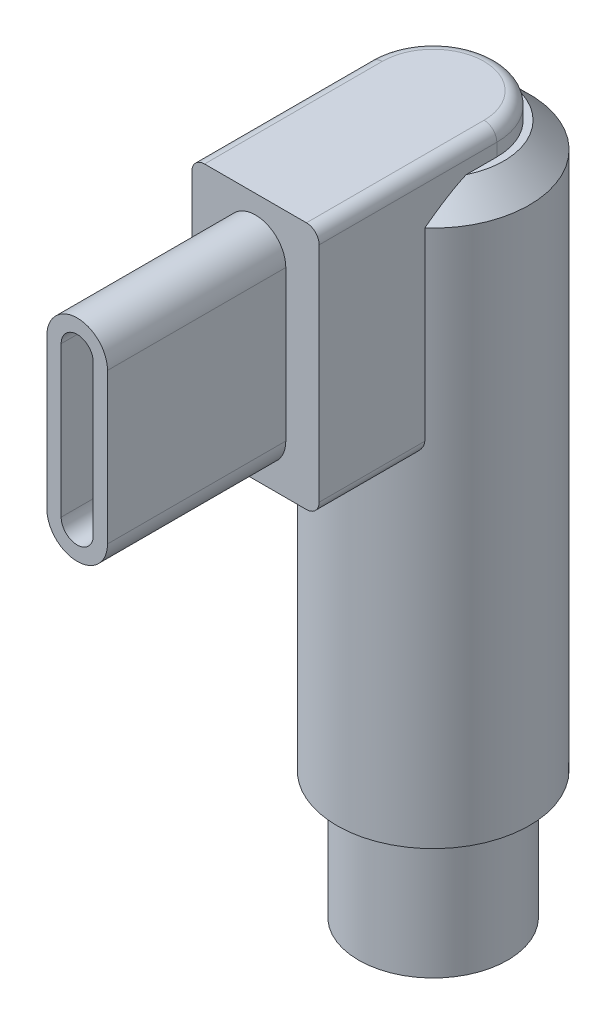
SolidWorks part; units mm, degrees
ref_plane "Front" through (0, 0, 0) normal (0, 0, 1) x (1, 0, 0)
ref_plane "Top" through (0, 0, 0) normal (0, 1, 0) x (1, 0, 0)
ref_plane "Right" through (0, 0, 0) normal (1, 0, 0) x (0, 0, -1)
sketch "Sketch1" plane through (0, 0, 0) normal (0, 1, 0) x (1, 0, 0)
  circle A0 centre (0, 0) radius 2.925
  dimension "D1" = 5.85
extrude "Boss-Extrude1" add sketch "Sketch1" along normal blind 5
sketch "Sketch2" plane through (0, 5, 0) normal (0, 1, 0) x (1, 0, 0)
  circle A0 centre (0, 0) radius 3.775
  dimension "D1" = 7.55
extrude "Boss-Extrude2" add sketch "Sketch2" along normal blind 23.1
ref_plane "Plane1" through (0, 0, 3.775) normal (0, 0, 1) x (1, 0, 0)
sketch "Sketch3" plane through (0, 0, 3.775) normal (0, 0, 1) x (1, 0, 0)
  line L0 (3.775, 28.1) -> (-3.775, 28.1) construction
  line L1 (-2.5, 28.1) -> (2.5, 28.1)
  line L2 (-2.5, 28.1) -> (-2.5, 18.35)
  line L3 (-2.5, 18.35) -> (2.5, 18.35)
  line L4 (2.5, 28.1) -> (2.5, 18.35)
  point P4 (0, 28.1)
  dimension "D1" = 5
  dimension "D2" = 9.75
extrude "Boss-Extrude3" add sketch "Sketch3" along normal blind 3.2 and the other way up to next
sketch "Sketch4" plane through (0, 0, 6.975) normal (0, 0, 1) x (1, 0, 0)
  line L0 (0, 26.175) -> (0, 20.275) construction
  line L1 (1.19, 26.175) -> (1.19, 20.275)
  line L2 (-1.19, 26.175) -> (-1.19, 20.275)
  line L3 (-2.5, 23.225) -> (0, 23.225) construction
  line L4 (-2.5, 28.1) -> (-2.5, 18.35) construction
  line L5 (0, 26.175) -> (0, 20.275) construction
  line L6 (0.63, 26.175) -> (0.63, 20.275)
  line L7 (-0.63, 26.175) -> (-0.63, 20.275)
  arc A0 (1.19, 26.175) -> (-1.19, 26.175) centre (0, 26.175) ccw
  arc A1 (-1.19, 20.275) -> (1.19, 20.275) centre (0, 20.275) ccw
  arc A2 (0.63, 26.175) -> (-0.63, 26.175) centre (0, 26.175) ccw
  arc A3 (-0.63, 20.275) -> (0.63, 20.275) centre (0, 20.275) ccw
  point P3 (0, 23.225)
  point P8 (0, 27.365)
  point P9 (0, 19.085)
  point P16 (0, 23.225)
  dimension "D1" = 8.28
  dimension "D2" = 2.38
  dimension "D3" = 0.56
extrude "Boss-Extrude4" add sketch "Sketch4" along normal blind 7
sketch "Sketch5" plane through (0, 28.1, 0) normal (0, 1, 0) x (1, 0, 0)
  line L0 (2.5, 0) -> (2.5, -2.8285)
  line L1 (-2.5, 0) -> (-2.5, -2.8285)
  line L5 (-2.5, -2.8285) -> (-2.5, -6.975)
  line L6 (-2.5, -6.975) -> (2.5, -6.975)
  line L7 (2.5, -6.975) -> (2.5, -2.8285)
  arc A0 (2.5, 0) -> (-2.5, 0) centre (0, 0) ccw
  arc A2 (2.5, -2.8285) -> (-2.5, -2.8285) centre (0, 0) ccw
  arc A3 (2.5, -2.8285) -> (-2.5, -2.8285) centre (0, 0) ccw
  dimension "D1" = 0
extrude "Cut-Extrude1" cut sketch "Sketch5" against normal blind 1
chamfer "Chamfer1" distance 1 angle 45 1 edges at (0, 27.1, -3.775)
fillet "Fillet1" radius 0.5 5 edges at (-2.5, 18.35, 4.9018) (-2.5, 28.1, 3.4875) (0, 28.1, -2.5) (2.5, 18.35, 4.9018) (2.5, 28.1, 3.4875)
